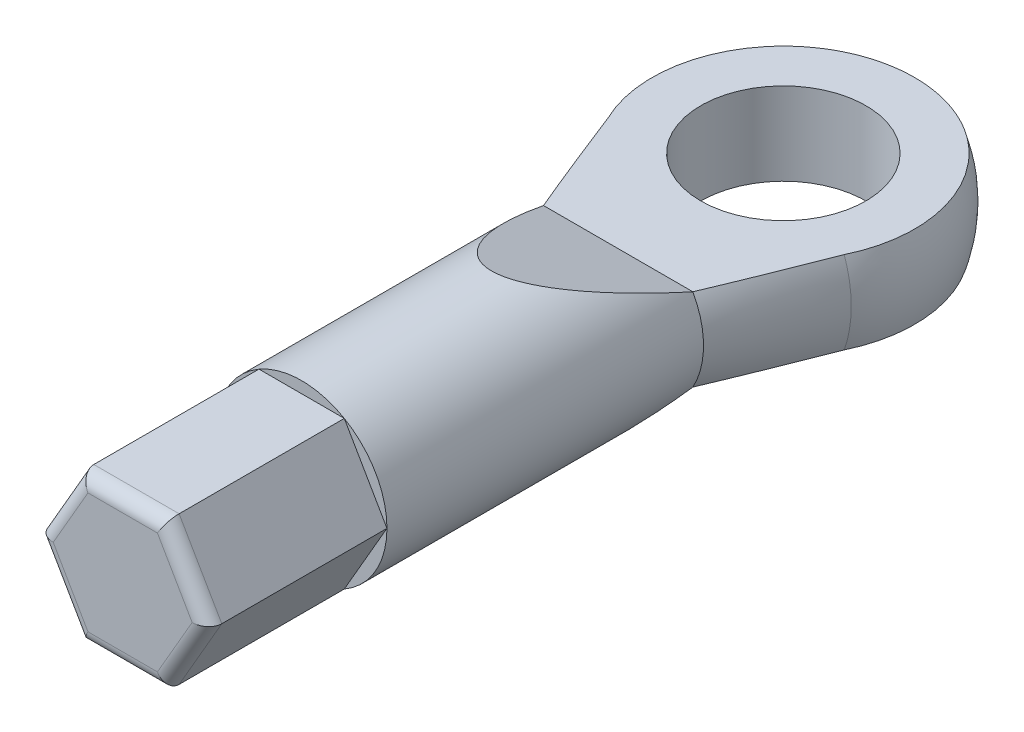
SolidWorks part; units mm, degrees
material "ABS"
ref_plane "Front Plane" through (0, 0, 0) normal (0, 0, 1) x (1, 0, 0)
ref_plane "Top Plane" through (0, 0, 0) normal (0, 1, 0) x (1, 0, 0)
ref_plane "Right Plane" through (0, 0, 0) normal (1, 0, 0) x (0, 0, -1)
sketch "Sketch1" plane through (0, 0, 0) normal (0, 1, 0) x (1, 0, 0)
  line L0 (0, 29) -> (0, 0) construction
  line L1 (0, 0) -> (-3.1, 0)
  line L2 (-3.1, 0) -> (-3.1, 18)
  line L3 (-4.5466, 21.9195) -> (-3.1, 18)
  arc A1 (0, 29) -> (0, 19) centre (0, 24) ccw
  point P1 (0, 29)
  dimension "D1" = 10
  dimension "D2" = 29
  dimension "D3" = 3.1
  dimension "D4" = 18
  dimension "D5" = 3.9195
  dimension "D6" = 24
  dimension "D7" = 5
revolve "Revolve1" add sketch "Sketch1" angle 360 about L0
sketch "Sketch2" plane through (0, 0, 0) normal (1, 0, 0) x (0, 0, -1)
  line L0 (0, 0) -> (29, 0) construction
  line L1 (18, -3.1) -> (21.9195, -4.5466) construction
  line L2 (28.7697, -1.5) -> (18, -1.5)
  line L3 (18, 1.5) -> (13.4003, 3.1)
  line L4 (28.7697, 1.5) -> (18, 1.5)
  line L5 (18, 3.1) -> (18, -3.1) construction
  line L6 (18, 3.1) -> (0, 3.1) construction
  line L7 (18, -3.1) -> (21.9195, -4.5466)
  line L8 (18, -1.5) -> (13.4003, -3.1)
  line L10 (0, -3.1) -> (18, -3.1) construction
  line L11 (13.4003, 3.1) -> (18, 3.1)
  line L12 (18, 3.1) -> (21.9195, 4.5466)
  line L13 (13.4003, -3.1) -> (18, -3.1)
  arc A0 (21.9195, -4.5466) -> (21.9195, 4.5466) centre (24, 0) ccw construction
  arc A1 (28.7697, -1.5) -> (28.7697, 1.5) centre (24, 0) ccw
  arc A2 (21.9195, -4.5466) -> (21.9195, 4.5466) centre (24, 0) ccw
  dimension "D1" = 3
  dimension "D2" = 19.18
  dimension "D3" = 19.18
extrude "Cut-Extrude2" cut sketch "Sketch2" against normal mid plane 12 contours L4 A2 L12 L11 L3 | L7 A2 L2 L8 L13
sketch "Sketch4" plane through (0, 0, 0) normal (0, 0, 1) x (1, 0, 0)
  line L1 (1.55, 2.6847) -> (-1.55, 2.6847)
  line L2 (-1.55, 2.6847) -> (-3.1, 0)
  line L3 (-3.1, 0) -> (-1.55, -2.6847)
  line L4 (-1.55, -2.6847) -> (1.55, -2.6847)
  line L5 (1.55, -2.6847) -> (3.1, 0)
  line L6 (3.1, 0) -> (1.55, 2.6847)
  circle A0 centre (0, 0) radius 2.6847 construction
  circle A1 centre (0, 0) radius 3.1 construction
  dimension "D1" = 5.3694
extrude "Cut-Extrude3" cut sketch "Sketch4" against normal blind 6.5 flip side to cut
fillet "Fillet1" radius 0.5 6 edges at (2.325, -1.3423, 0) (0, -2.6847, 0) (-2.325, -1.3423, 0) (-2.325, 1.3423, 0) (0, 2.6847, 0) (2.325, 1.3423, 0)
sketch "Sketch5" plane through (0, 1.5, 0) normal (0, 1, 0) x (1, 0, 0)
  line L0 (0, 0) -> (0, 29.9603) construction
  line L1 (-7.0376, 24) -> (7.0935, 24) construction
  circle A0 centre (0, 24) radius 3
  dimension "D1" = 6
  dimension "D2" = 24
extrude "Cut-Extrude4" cut sketch "Sketch5" against normal mid plane 3 from offset 1.5 offset against normal yes
sketch "Sketch6" plane through (0, 0, 0) normal (1, 0, 0) x (0, 0, -1)
  line L0 (24, 1.5) -> (24, 0) construction
  line L1 (27, 1.5) -> (21, 1.5)
  line L2 (27, 1.5) -> (21, 1.5)
  dimension "D2" = 1.5
  dimension "D1" = 0
sketch3d "3DSketch1"
  point P0 (0, 0, -24)
sketch "Sketch7" plane through (0, 0, 0) normal (0, 1, 0) x (1, 0, 0)
  line L0 (0, 27) -> (0, 21) construction
  line L1 (0, 27) -> (0, 21)
  line L2 (-6.2541, 24) -> (7.2614, 24) construction
  point P2 (0, 24)
sketch3d "3DSketch2"
  line L0 (0, 0, 0) -> (0, 0, 220.1123) construction
  line L1 (0, 0, -29) -> (0, 0, 0) construction
sketch3d "3DSketch3"
  line L0 (0, 0, -24) -> (-5, 0, -24) construction
  arc A0 (0, 0, -29) -> (0, 0, -19) centre (0, 0, -24) ccw construction
  point P6 (0, 5, -24)
